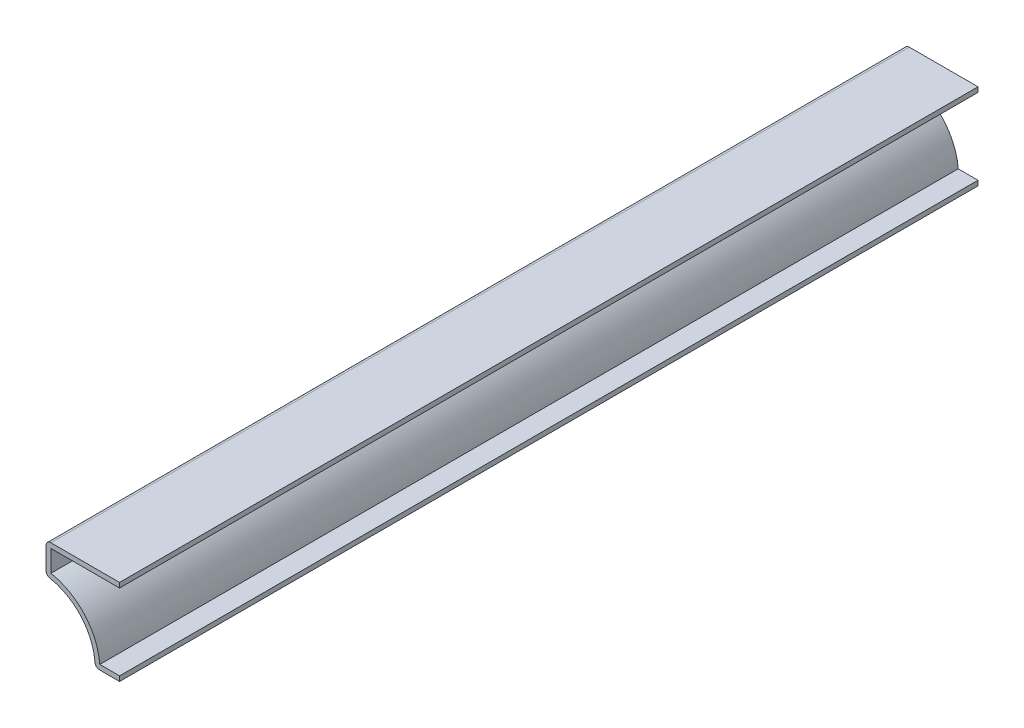
SolidWorks part; units mm, degrees
ref_plane "Front Plane" through (0, 0, 0) normal (0, 0, 1) x (1, 0, 0)
ref_plane "Top Plane" through (0, 0, 0) normal (0, 1, 0) x (1, 0, 0)
ref_plane "Right Plane" through (0, 0, 0) normal (1, 0, 0) x (0, 0, -1)
sketch "Sketch1" plane through (0, 0, 0) normal (0, 0, 1) x (1, 0, 0)
  line L0 (0, 0) -> (-6.35, 0)
  line L1 (-19.05, 14.2875) -> (-19.05, 22.225)
  line L2 (-19.05, 22.225) -> (0, 22.225)
  arc A0 (-6.35, 0) -> (-19.05, 14.2875) centre (-20.6372, 0.0884) ccw
  point P5 (0, 0)
  dimension "D2" = 14.2875
  dimension "D1" = 6.35
  dimension "D3" = 7.9375
  dimension "D4" = 22.225
  dimension "D5" = 12.7
  dimension "D6" = 14.2875
  dimension "D7" = 19.05
extrude "Extrude-Thin1" add sketch "Sketch1" against normal blind 222.25 thin
fillet "Fillet1" radius 1.27 3 edges at (-6.35, 0, -111.125) (-19.05, 14.2875, -111.125) (-19.05, 22.225, -111.125)
